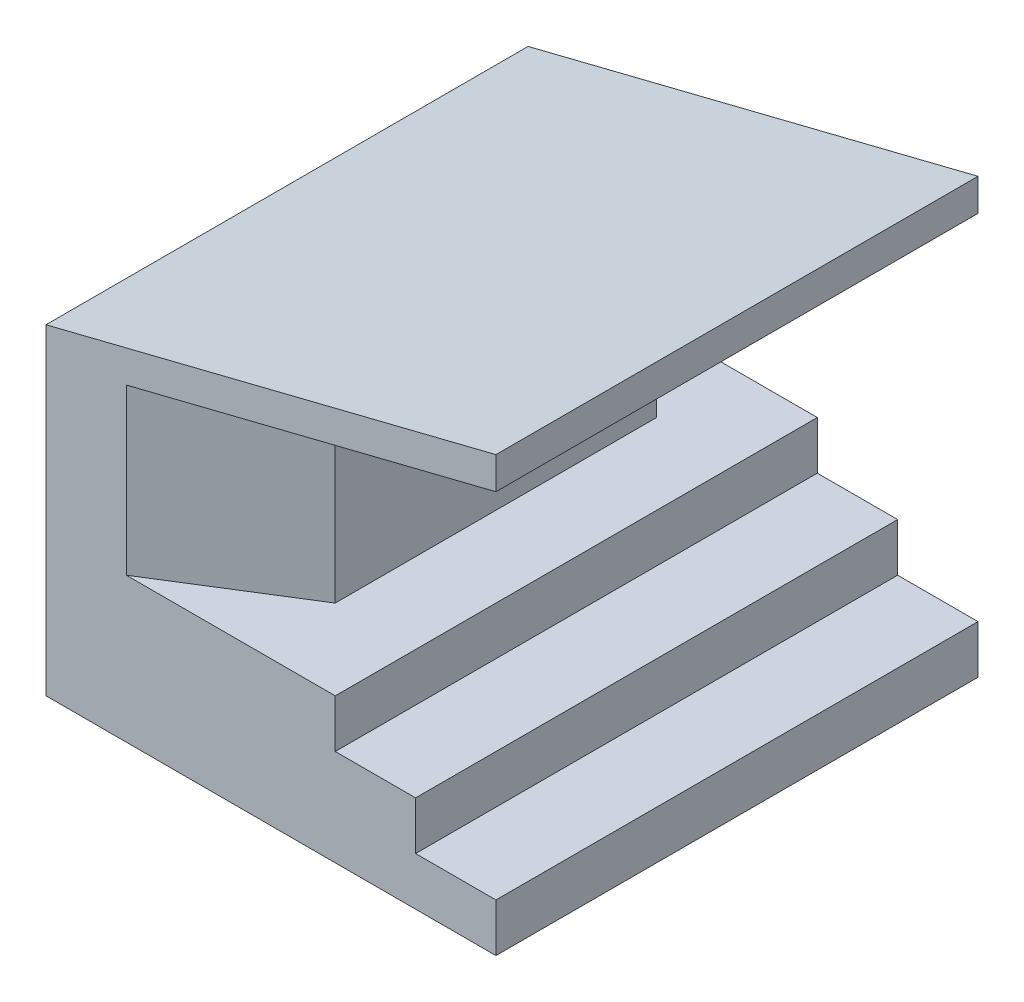
SolidWorks part; units mm, degrees
other "Perspective"
ref_plane "Front Plane" through (0, 0, 0) normal (0, 0, 1) x (1, 0, 0)
ref_plane "Top Plane" through (0, 0, 0) normal (0, 1, 0) x (1, 0, 0)
ref_plane "Right Plane" through (0, 0, 0) normal (1, 0, 0) x (0, 0, -1)
sketch "Sketch1" plane through (0, 0, 0) normal (0, 1, 0) x (1, 0, 0)
  line L1 (0, 0) -> (-140, 0)
  line L2 (0, 0) -> (0, 150)
  line L3 (0, 150) -> (-140, 150)
  line L4 (-140, 0) -> (-140, 150)
  dimension "D1" = 150
  dimension "D2" = 140
extrude "Extrude1" add sketch "Sketch1" along normal blind 15
sketch "Sketch2" plane through (0, 0, 0) normal (0, 0, 1) x (1, 0, 0)
  line L0 (-25, 15) -> (-25, 30)
  line L1 (-140, 15) -> (0, 15) construction
  line L2 (-25, 30) -> (-50, 30)
  line L3 (-50, 30) -> (-50, 45)
  line L4 (-50, 45) -> (-115, 45)
  line L5 (-115, 45) -> (-115, 96.25)
  line L6 (-115, 96.25) -> (0, 125)
  line L7 (0, 125) -> (0, 135)
  line L8 (0, 135) -> (-140, 100)
  line L9 (-140, 100) -> (-140, 15)
  line L10 (-25, 15) -> (-140, 15)
  dimension "D1" = 100
  dimension "D2" = 15
  dimension "D3" = 15
  dimension "D4" = 65
  dimension "D5" = 25
  dimension "D6" = 25
  dimension "D7" = 10
  dimension "D8" = 135
extrude "Extrude2" add sketch "Sketch2" against normal blind 150
sketch "Sketch3" plane through (0, 45, 0) normal (0, 1, 0) x (1, 0, 0)
  line L0 (-115, 150) -> (-75, 125)
  line L1 (-75, 125) -> (-75, 25)
  line L2 (-75, 25) -> (-115, 0)
  line L3 (-115, 0) -> (-115, 150)
  line L4 (0, 150) -> (-140, 150) construction
  line L5 (0, 0) -> (-140, 0) construction
  point P8 (-70, 0)
  dimension "D1" = 25
  dimension "D2" = 25
  dimension "D3" = 40
extrude "Extrude3" add sketch "Sketch3" along normal up to surface (51.25 mm away)
